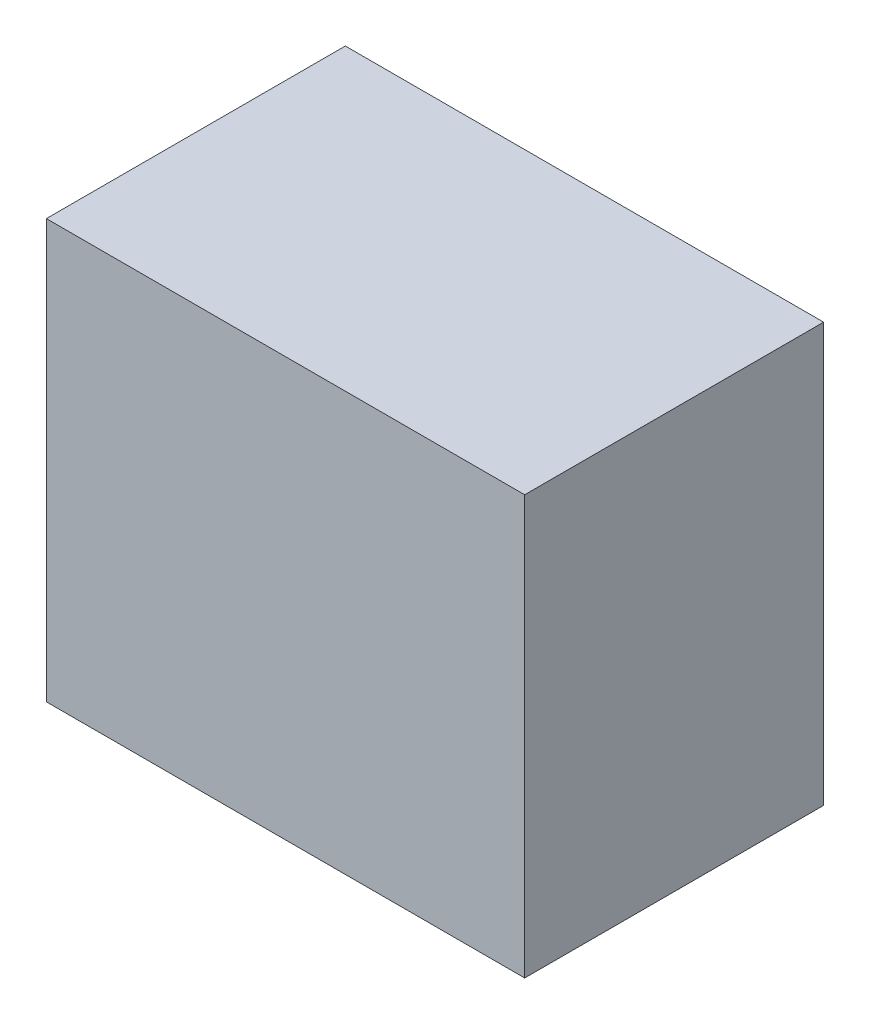
SolidWorks part; units mm, degrees
ref_plane "Front Plane" through (0, 0, 0) normal (0, 0, 1) x (1, 0, 0)
ref_plane "Top Plane" through (0, 0, 0) normal (0, 1, 0) x (1, 0, 0)
ref_plane "Right Plane" through (0, 0, 0) normal (1, 0, 0) x (0, 0, -1)
sketch "Sketch1" plane through (0, 0, 0) normal (0, 0, 1) x (1, 0, 0)
  line L1 (0, 0) -> (50.8, 0)
  line L2 (0, 0) -> (0, 44.45)
  line L3 (0, 44.45) -> (50.8, 44.45)
  line L4 (50.8, 0) -> (50.8, 44.45)
  dimension "D1" = 44.45
  dimension "D2" = 50.8
extrude "Boss-Extrude1" add sketch "Sketch1" along normal blind 31.75
